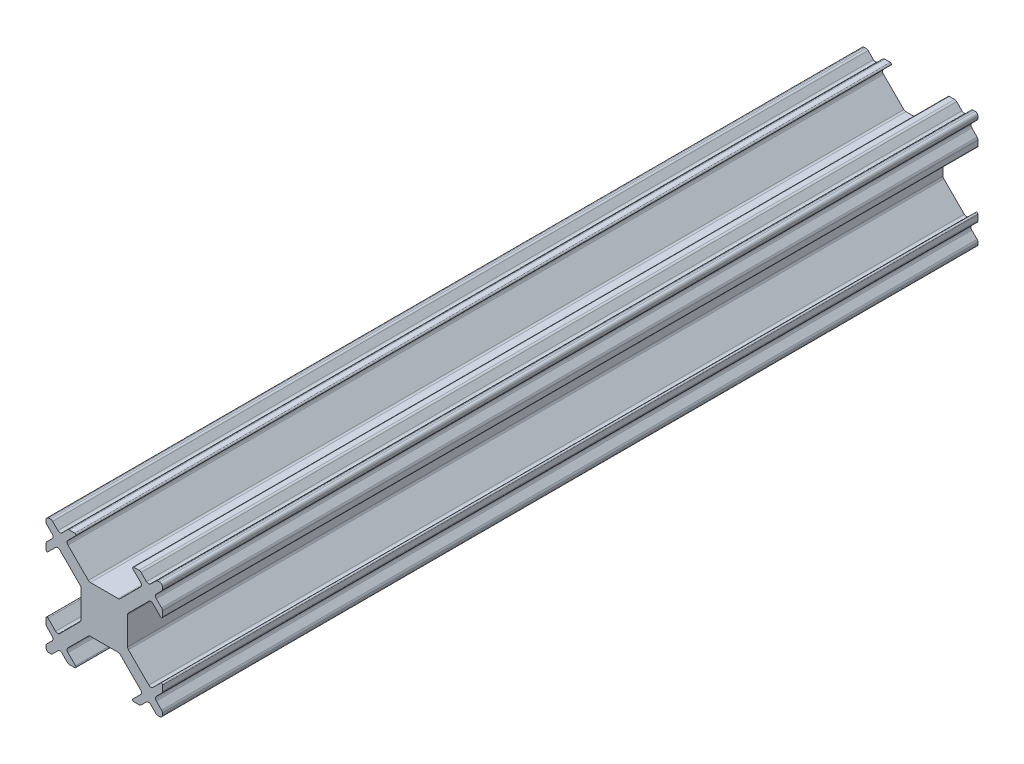
SolidWorks part; units mm, degrees
ref_plane "Front Plane" through (0, 0, 0) normal (0, 0, 1) x (1, 0, 0)
ref_plane "Top Plane" through (0, 0, 0) normal (0, 1, 0) x (1, 0, 0)
ref_plane "Right Plane" through (0, 0, 0) normal (1, 0, 0) x (0, 0, -1)
sketch "Sketch1" plane through (0, 0, 0) normal (0, 0, 1) x (1, 0, 0)
  line L0 (-26.4346, 28.4965) -> (-25.9796, 28.9515)
  line L1 (-25.1311, 29.8) -> (-24.676, 30.2551)
  line L2 (-24.676, 20.4015) -> (-25.1311, 20.8565)
  line L3 (-25.9796, 21.7051) -> (-26.4346, 22.1601)
  line L4 (-26.5078, 30.0783) -> (-26.5078, 29.9369)
  line L5 (-26.5078, 28.3197) -> (-26.5078, 27.8626)
  line L6 (-26.5078, 22.794) -> (-26.5078, 22.3369)
  line L7 (-26.5078, 20.7197) -> (-26.5078, 20.5783)
  line L8 (-23.9714, 30.1576) -> (-24.624, 29.5051)
  line L9 (-25.6846, 28.4444) -> (-26.3371, 27.7919)
  line L10 (-26.2578, 20.3283) -> (-26.1164, 20.3283)
  line L11 (-24.4993, 20.3283) -> (-24.0422, 20.3283)
  line L12 (-18.9735, 20.3283) -> (-18.5164, 20.3283)
  line L13 (-16.8993, 20.3283) -> (-16.7578, 20.3283)
  line L14 (-26.3371, 22.8647) -> (-25.6846, 22.2122)
  line L15 (-24.624, 21.1515) -> (-23.9714, 20.499)
  line L16 (-23.5078, 26.5176) -> (-23.5078, 24.139)
  line L17 (-22.6972, 23.3283) -> (-20.3185, 23.3283)
  line L18 (-25.3311, 22.2122) -> (-23.5811, 23.9622)
  line L19 (-20.1417, 27.4015) -> (-18.3917, 29.1515)
  line L20 (-18.3917, 21.5051) -> (-20.1417, 23.2551)
  line L21 (-23.5811, 26.6944) -> (-25.3311, 28.4444)
  line L22 (-26.4346, 20.8965) -> (-25.9796, 21.3515)
  line L23 (-17.5311, 29.8) -> (-17.076, 30.2551)
  line L24 (-17.076, 20.4015) -> (-17.5311, 20.8565)
  line L25 (-25.9796, 29.3051) -> (-26.4346, 29.7601)
  line L26 (-16.5811, 29.7601) -> (-17.0361, 29.3051)
  line L27 (-25.4846, 20.8565) -> (-25.9396, 20.4015)
  line L28 (-17.6846, 28.4444) -> (-19.4346, 26.6944)
  line L29 (-22.874, 23.2551) -> (-24.624, 21.5051)
  line L30 (-25.9396, 30.2551) -> (-25.4846, 29.8)
  line L31 (-17.0361, 21.3515) -> (-16.5811, 20.8965)
  line L32 (-24.624, 29.1515) -> (-22.874, 27.4015)
  line L33 (-19.4346, 23.9622) -> (-17.6846, 22.2122)
  line L34 (-19.5078, 24.139) -> (-19.5078, 26.5176)
  line L35 (-20.3185, 27.3283) -> (-22.6972, 27.3283)
  line L36 (-16.5078, 20.5783) -> (-16.5078, 20.7197)
  line L37 (-16.5078, 22.3369) -> (-16.5078, 22.794)
  line L38 (-16.5078, 27.8626) -> (-16.5078, 28.3197)
  line L39 (-16.5078, 29.9369) -> (-16.5078, 30.0783)
  line L40 (-16.7578, 30.3283) -> (-16.8993, 30.3283)
  line L41 (-18.5164, 30.3283) -> (-18.9735, 30.3283)
  line L42 (-24.0422, 30.3283) -> (-24.4993, 30.3283)
  line L43 (-26.1164, 30.3283) -> (-26.2578, 30.3283)
  line L44 (-19.0442, 20.499) -> (-18.3917, 21.1515)
  line L45 (-17.3311, 22.2122) -> (-16.6786, 22.8647)
  line L46 (-16.6786, 27.7919) -> (-17.3311, 28.4444)
  line L47 (-18.3917, 29.5051) -> (-19.0442, 30.1576)
  line L48 (-16.5811, 22.1601) -> (-17.0361, 21.7051)
  line L49 (-17.8846, 20.8565) -> (-18.3396, 20.4015)
  line L50 (-18.3396, 30.2551) -> (-17.8846, 29.8)
  line L51 (-17.0361, 28.9515) -> (-16.5811, 28.4965)
  arc A0 (-16.5078, 30.0783) -> (-16.7578, 30.3283) centre (-16.7578, 30.0783) ccw
  arc A1 (-26.2578, 30.3283) -> (-26.5078, 30.0783) centre (-26.2578, 30.0783) ccw
  arc A2 (-16.7578, 20.3283) -> (-16.5078, 20.5783) centre (-16.7578, 20.5783) ccw
  arc A3 (-26.5078, 20.5783) -> (-26.2578, 20.3283) centre (-26.2578, 20.5783) ccw
  arc A4 (-18.9735, 30.3283) -> (-19.0442, 30.1576) centre (-18.9735, 30.2283) ccw
  arc A5 (-16.6786, 27.7919) -> (-16.5078, 27.8626) centre (-16.6078, 27.8626) ccw
  arc A6 (-16.5078, 22.794) -> (-16.6786, 22.8647) centre (-16.6078, 22.794) ccw
  arc A7 (-19.0442, 20.499) -> (-18.9735, 20.3283) centre (-18.9735, 20.4283) ccw
  arc A8 (-26.3371, 22.8647) -> (-26.5078, 22.794) centre (-26.4078, 22.794) ccw
  arc A9 (-26.5078, 27.8626) -> (-26.3371, 27.7919) centre (-26.4078, 27.8626) ccw
  arc A10 (-23.9714, 30.1576) -> (-24.0422, 30.3283) centre (-24.0422, 30.2283) ccw
  arc A11 (-24.0422, 20.3283) -> (-23.9714, 20.499) centre (-24.0422, 20.4283) ccw
  arc A12 (-22.874, 27.4015) -> (-22.6972, 27.3283) centre (-22.6972, 27.5783) ccw
  arc A13 (-20.3185, 27.3283) -> (-20.1417, 27.4015) centre (-20.3185, 27.5783) ccw
  arc A14 (-19.5078, 24.139) -> (-19.4346, 23.9622) centre (-19.2578, 24.139) ccw
  arc A15 (-17.6846, 22.2122) -> (-17.3311, 22.2122) centre (-17.5078, 22.389) ccw
  arc A16 (-22.6972, 23.3283) -> (-22.874, 23.2551) centre (-22.6972, 23.0783) ccw
  arc A17 (-20.1417, 23.2551) -> (-20.3185, 23.3283) centre (-20.3185, 23.0783) ccw
  arc A18 (-25.3311, 28.4444) -> (-25.6846, 28.4444) centre (-25.5078, 28.2676) ccw
  arc A19 (-23.5811, 23.9622) -> (-23.5078, 24.139) centre (-23.7578, 24.139) ccw
  arc A20 (-23.5078, 26.5176) -> (-23.5811, 26.6944) centre (-23.7578, 26.5176) ccw
  arc A21 (-25.6846, 22.2122) -> (-25.3311, 22.2122) centre (-25.5078, 22.389) ccw
  arc A22 (-24.624, 21.5051) -> (-24.624, 21.1515) centre (-24.4472, 21.3283) ccw
  arc A23 (-18.3917, 21.1515) -> (-18.3917, 21.5051) centre (-18.5685, 21.3283) ccw
  arc A24 (-18.3917, 29.1515) -> (-18.3917, 29.5051) centre (-18.5685, 29.3283) ccw
  arc A25 (-17.3311, 28.4444) -> (-17.6846, 28.4444) centre (-17.5078, 28.2676) ccw
  arc A26 (-19.4346, 26.6944) -> (-19.5078, 26.5176) centre (-19.2578, 26.5176) ccw
  arc A27 (-24.624, 29.5051) -> (-24.624, 29.1515) centre (-24.4472, 29.3283) ccw
  arc A28 (-17.0361, 29.3051) -> (-17.0361, 28.9515) centre (-16.8593, 29.1283) ccw
  arc A29 (-17.0361, 21.7051) -> (-17.0361, 21.3515) centre (-16.8593, 21.5283) ccw
  arc A30 (-25.4846, 29.8) -> (-25.1311, 29.8) centre (-25.3078, 29.9768) ccw
  arc A31 (-17.8846, 29.8) -> (-17.5311, 29.8) centre (-17.7078, 29.9768) ccw
  arc A32 (-25.9796, 28.9515) -> (-25.9796, 29.3051) centre (-26.1564, 29.1283) ccw
  arc A33 (-25.9796, 21.3515) -> (-25.9796, 21.7051) centre (-26.1564, 21.5283) ccw
  arc A34 (-17.5311, 20.8565) -> (-17.8846, 20.8565) centre (-17.7078, 20.6798) ccw
  arc A35 (-25.1311, 20.8565) -> (-25.4846, 20.8565) centre (-25.3078, 20.6798) ccw
  arc A36 (-18.3396, 30.2551) -> (-18.5164, 30.3283) centre (-18.5164, 30.0783) ccw
  arc A37 (-16.8993, 30.3283) -> (-17.076, 30.2551) centre (-16.8993, 30.0783) ccw
  arc A38 (-24.4993, 30.3283) -> (-24.676, 30.2551) centre (-24.4993, 30.0783) ccw
  arc A39 (-25.9396, 30.2551) -> (-26.1164, 30.3283) centre (-26.1164, 30.0783) ccw
  arc A40 (-26.5078, 29.9369) -> (-26.4346, 29.7601) centre (-26.2578, 29.9369) ccw
  arc A41 (-26.4346, 28.4965) -> (-26.5078, 28.3197) centre (-26.2578, 28.3197) ccw
  arc A42 (-26.4346, 20.8965) -> (-26.5078, 20.7197) centre (-26.2578, 20.7197) ccw
  arc A43 (-26.5078, 22.3369) -> (-26.4346, 22.1601) centre (-26.2578, 22.3369) ccw
  arc A44 (-24.676, 20.4015) -> (-24.4993, 20.3283) centre (-24.4993, 20.5783) ccw
  arc A45 (-18.5164, 20.3283) -> (-18.3396, 20.4015) centre (-18.5164, 20.5783) ccw
  arc A46 (-17.076, 20.4015) -> (-16.8993, 20.3283) centre (-16.8993, 20.5783) ccw
  arc A47 (-16.5078, 28.3197) -> (-16.5811, 28.4965) centre (-16.7578, 28.3197) ccw
  arc A48 (-16.5078, 20.7197) -> (-16.5811, 20.8965) centre (-16.7578, 20.7197) ccw
  arc A49 (-16.5811, 22.1601) -> (-16.5078, 22.3369) centre (-16.7578, 22.3369) ccw
  arc A50 (-16.5811, 29.7601) -> (-16.5078, 29.9369) centre (-16.7578, 29.9369) ccw
  arc A51 (-26.1164, 20.3283) -> (-25.9396, 20.4015) centre (-26.1164, 20.5783) ccw
  dimension "D1" = 4
  dimension "D2" = 10
extrude "Boss-Extrude1" add sketch "Sketch1" along normal blind 70
